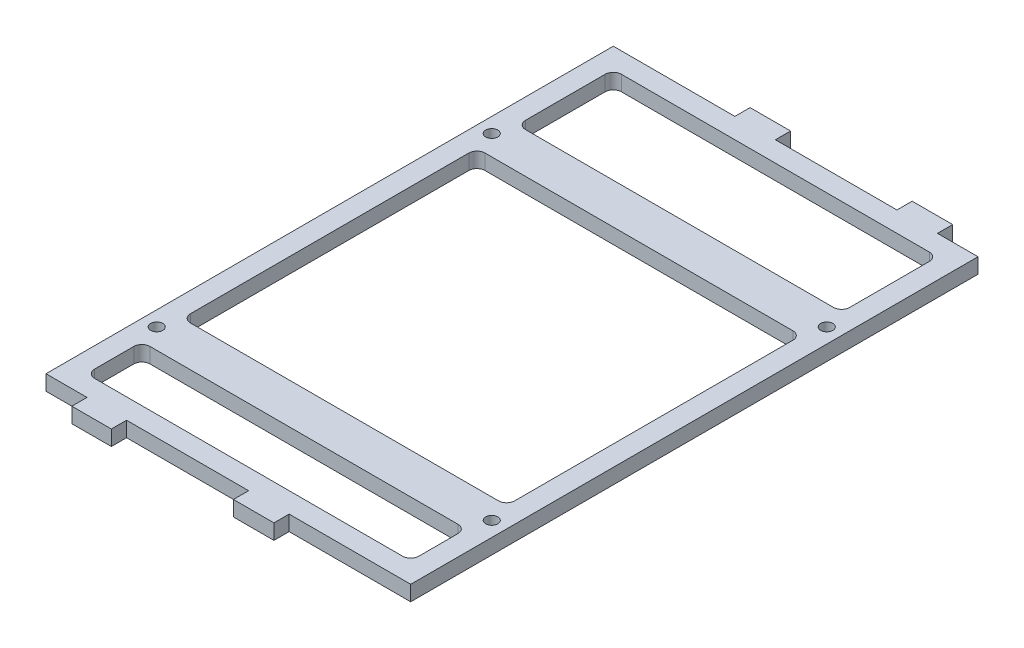
SolidWorks part; units mm, degrees
material "6061-T6 (SS)"
ref_plane "Front Plane" through (0, 0, 0) normal (0, 0, 1) x (1, 0, 0)
ref_plane "Top Plane" through (0, 0, 0) normal (0, 1, 0) x (1, 0, 0)
ref_plane "Right Plane" through (0, 0, 0) normal (1, 0, 0) x (0, 0, -1)
sketch "Sketch1" plane through (0, 0, 0) normal (0, 1, 0) x (1, 0, 0)
  line L0 (50.8, 82.55) -> (-50.8, 82.55)
  line L1 (57.15, 88.9) -> (-57.15, 88.9)
  line L2 (57.15, 88.9) -> (57.15, -88.9)
  line L3 (57.15, -88.9) -> (-57.15, -88.9)
  line L4 (-57.15, 88.9) -> (-57.15, -88.9)
  line L5 (57.15, 88.9) -> (-57.15, -88.9) construction
  line L6 (57.15, -88.9) -> (-57.15, 88.9) construction
  line L7 (-50.8, 82.55) -> (-50.8, -82.55)
  line L8 (50.8, -82.55) -> (-50.8, -82.55)
  line L9 (50.8, 82.55) -> (50.8, -82.55)
  point P0 (0, 0)
  dimension "D1" = 114.3
  dimension "D2" = 177.8
  dimension "D3" = 6.35
extrude "Boss-Extrude1" add sketch "Sketch1" along normal blind 4.7625
sketch "Sketch2" plane through (0, 0, 88.9) normal (0, 0, 1) x (1, 0, 0)
  line L0 (-57.15, 2.3813) -> (57.15, 2.3813) construction
  line L1 (-57.15, 4.7625) -> (-57.15, 0) construction
  line L2 (57.15, 4.7625) -> (57.15, 0) construction
  line L3 (-57.15, 0) -> (57.15, 0) construction
  line L4 (-31.9066, 4.7625) -> (-44.2934, 4.7625)
  line L5 (-31.9066, 4.7625) -> (-31.9066, 0)
  line L6 (-31.9066, 0) -> (-44.2934, 0)
  line L7 (-44.2934, 4.7625) -> (-44.2934, 0)
  line L8 (-31.9066, 4.7625) -> (-44.2934, 0) construction
  line L9 (-31.9066, 0) -> (-44.2934, 4.7625) construction
  line L11 (19.05, 4.7625) -> (6.35, 4.7625)
  line L12 (19.05, 4.7625) -> (19.05, 0)
  line L13 (19.05, 0) -> (6.35, 0)
  line L14 (6.35, 4.7625) -> (6.35, 0)
  line L15 (19.05, 4.7625) -> (6.35, 0) construction
  line L16 (19.05, 0) -> (6.35, 4.7625) construction
  point P6 (-38.1, 2.3813)
  point P13 (12.7, 2.3813)
  dimension "D1" = 19.05
  dimension "D2" = 50.8
  dimension "D3" = 12.7
extrude "Boss-Extrude2" add sketch "Sketch2" along normal blind 4.7625
sketch "Sketch3" plane through (0, 0, -88.9) normal (0, 0, -1) x (-1, 0, 0)
  line L0 (-57.15, 2.3813) -> (57.15, 2.3813) construction
  line L1 (-57.15, 4.7625) -> (-57.15, 0) construction
  line L2 (57.15, 4.7625) -> (57.15, 0) construction
  line L3 (-57.15, 0) -> (57.15, 0) construction
  line L4 (-31.75, 4.7625) -> (-44.45, 4.7625)
  line L5 (-31.75, 4.7625) -> (-31.75, 0)
  line L6 (-31.75, 0) -> (-44.45, 0)
  line L7 (-44.45, 4.7625) -> (-44.45, 0)
  line L8 (-31.75, 4.7625) -> (-44.45, 0) construction
  line L9 (-31.75, 0) -> (-44.45, 4.7625) construction
  line L11 (19.05, 4.7625) -> (6.35, 4.7625)
  line L12 (19.05, 4.7625) -> (19.05, 0)
  line L13 (19.05, 0) -> (6.35, 0)
  line L14 (6.35, 4.7625) -> (6.35, 0)
  line L15 (19.05, 4.7625) -> (6.35, 0) construction
  line L16 (19.05, 0) -> (6.35, 4.7625) construction
  point P6 (-38.1, 2.3812)
  point P13 (12.7, 2.3812)
  dimension "D1" = 12.7
  dimension "D2" = 12.7
  dimension "D3" = 19.05
  dimension "D4" = 50.8
extrude "Boss-Extrude3" add sketch "Sketch3" along normal blind 4.7625
fillet "Fillet1" radius 2.54 4 edges at (50.8, 2.3813, 82.55) (50.8, 2.3813, -82.55) (-50.8, 2.3813, -82.55) (-50.8, 2.3813, 82.55)
sketch "Sketch4" plane through (0, 4.7625, 0) normal (0, 1, 0) x (1, 0, 0)
  line L0 (0, 82.55) -> (0, -82.55) construction
  line L1 (48.26, 82.55) -> (-48.26, 82.55) construction
  line L2 (-48.26, -82.55) -> (48.26, -82.55) construction
  line L3 (-57.15, 88.9) -> (-57.15, -88.9) construction
  line L4 (57.15, 52.5) -> (-57.15, 52.5)
  line L5 (57.15, 52.5) -> (57.15, 39.8)
  line L6 (57.15, 39.8) -> (-57.15, 39.8)
  line L7 (-57.15, 52.5) -> (-57.15, 39.8)
  line L8 (57.15, 52.5) -> (-57.15, 39.8) construction
  line L9 (57.15, 39.8) -> (-57.15, 52.5) construction
  line L11 (57.15, -52.5) -> (-57.15, -52.5)
  line L12 (57.15, -52.5) -> (57.15, -65.2)
  line L13 (57.15, -65.2) -> (-57.15, -65.2)
  line L14 (-57.15, -52.5) -> (-57.15, -65.2)
  line L15 (57.15, -52.5) -> (-57.15, -65.2) construction
  line L16 (57.15, -65.2) -> (-57.15, -52.5) construction
  point P6 (0, 46.15)
  point P13 (0, -58.85)
  dimension "D1" = 12.7
  dimension "D2" = 12.7
  dimension "D3" = 46.15
  dimension "D4" = 58.85
extrude "Boss-Extrude4" add sketch "Sketch4" against normal blind 4.7625
hole_wizard "#6 Clearance Hole1" positions "Sketch6" profile "Sketch5" hole size "#6" standard "Ansi Inch"
sketch "Sketch6" plane through (0, 4.7625, 0) normal (0, 1, 0) x (-1, 0, 0)
  line L0 (50.8, -52.5) -> (50.8, -39.8) construction
  line L2 (50.8, -46.15) -> (-57.15, -46.15) construction
  line L3 (-57.15, 88.9) -> (-57.15, -88.9) construction
  line L5 (50.8, 65.2) -> (50.8, 52.5) construction
  line L7 (0, 65.2) -> (0, 52.5) construction
  line L8 (50.8, 65.2) -> (-50.8, 65.2) construction
  line L9 (-50.8, 52.5) -> (50.8, 52.5) construction
  line L11 (50.8, 58.85) -> (-57.15, 58.85) construction
  point P0 (52.5, -46.15)
  point P1 (-52.5, -46.15)
  point P3 (52.5, 58.85)
  point P5 (-52.5, 58.85)
  dimension "D1" = 52.5
  dimension "D2" = 52.5
  dimension "D3" = 52.5
  dimension "D4" = 52.5
sketch "Sketch5" plane through (-52.5, 4.7625, -46.15) normal (1, 0, 0) x (0, 0, 1)
  line L0 (0, 0) -> (0, 26.5408)
  line L1 (0, 26.5408) -> (1.8986, 25.4)
  line L2 (1.8986, 25.4) -> (1.8986, 0)
  line L5 (1.8986, 0) -> (0, 0)
  line L10 (0, 26.5408) -> (-1.8987, 25.4) construction
  line L11 (0, -6.35) -> (0, 107.95) construction
  dimension "Hole Dia." = 3.7973
  dimension "Hole Depth" = 25.4
  dimension "Drill Angle" = 118
fillet "Fillet2" radius 2.54 8 edges at (-50.8, 2.3813, -52.5) (-50.8, 2.3813, -39.8) (50.8, 2.3813, -52.5) (50.8, 2.3813, -39.8) (50.8, 2.3813, 52.5) (-50.8, 2.3813, 52.5) (-50.8, 2.3813, 65.2) (50.8, 2.3813, 65.2)
